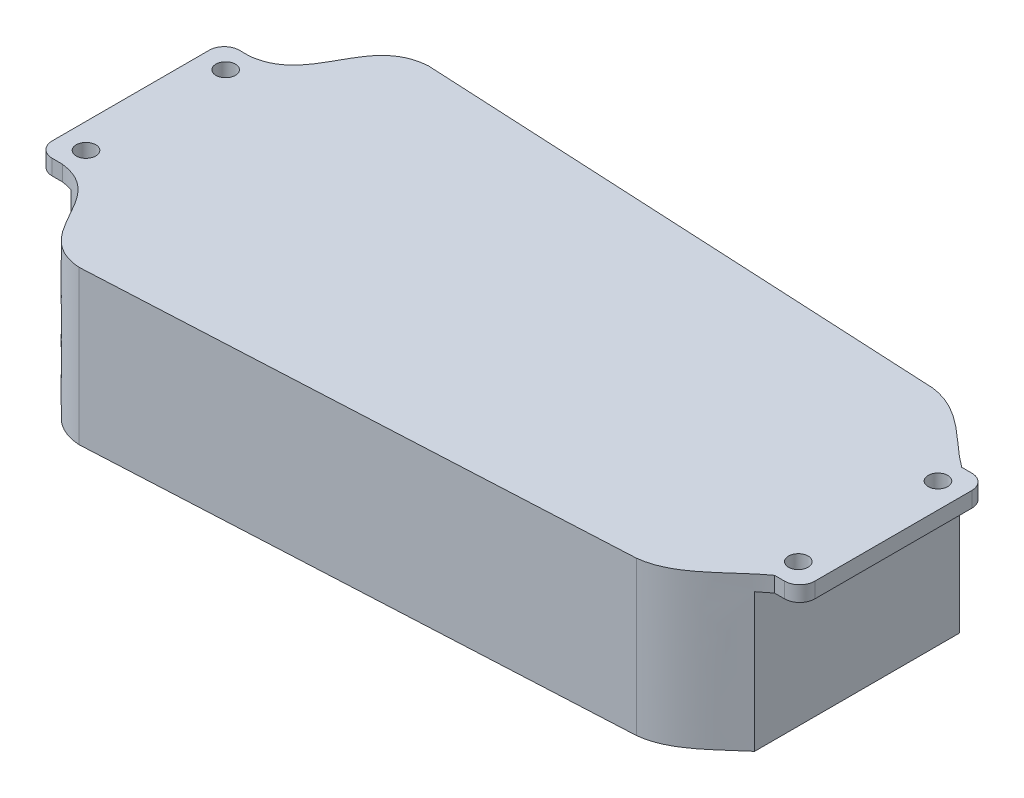
SolidWorks part; units mm, degrees
ref_plane "Front Plane" through (0, 0, 0) normal (0, 0, 1) x (1, 0, 0)
ref_plane "Top Plane" through (0, 0, 0) normal (0, 1, 0) x (1, 0, 0)
ref_plane "Right Plane" through (0, 0, 0) normal (1, 0, 0) x (0, 0, -1)
sketch "Sketch1" plane through (0, 0, 0) normal (0, 1, 0) x (1, 0, 0)
  line L0 (-77.2974, -66.9431) -> (112.638, -57.3431)
  line L2 (-121.2974, 23.6569) -> (-121.2974, -32.5431)
  line L4 (151.7026, 23.6569) -> (151.7026, -32.5431)
  line L5 (-115.7974, -37.9431) -> (-115.8974, -37.9431)
  line L6 (-115.7974, -37.9431) -> (-112.2974, -37.9431)
  line L7 (-77.2974, 58.0569) -> (112.638, 48.4569)
  line L8 (146.2026, -37.9431) -> (142.7026, -37.9431)
  line L9 (-115.7974, 29.0569) -> (-112.2974, 29.0569)
  line L10 (-115.7974, 29.0569) -> (-115.8974, 29.0569)
  line L11 (146.2026, 29.0569) -> (142.7026, 29.0569)
  line L12 (146.2026, 29.0569) -> (146.3026, 29.0569)
  line L13 (146.2026, -37.9431) -> (146.3026, -37.9431)
  circle A0 centre (-112.2974, 20.5569) radius 3.5
  circle A1 centre (-112.2974, -29.4431) radius 3.5
  circle A2 centre (142.7026, -29.4431) radius 3.5
  circle A3 centre (142.7026, 20.5569) radius 3.5
  arc A4 (-115.8974, -37.9431) -> (-121.2974, -32.5431) centre (-115.8974, -32.5431) cw
  arc A5 (-115.8974, 29.0569) -> (-121.2974, 23.6569) centre (-115.8974, 23.6569) ccw
  arc A6 (146.3026, -37.9431) -> (151.7026, -32.5431) centre (146.3026, -32.5431) ccw
  arc A7 (146.3026, 29.0569) -> (151.7026, 23.6569) centre (146.3026, 23.6569) cw
  spline S0 degree 3 poles (-77.2974, 58.0569) (-97.4783, 56.5585) (-92.6699, 31.2994) (-112.2974, 29.0569) knots 0 0 0 0 1 1 1 1
  spline S1 degree 3 poles (-77.2974, -66.9431) (-97.4783, -65.4448) (-92.6699, -40.1856) (-112.2974, -37.9431) knots 0 0 0 0 1 1 1 1
  spline S2 degree 3 poles (112.638, 48.4569) (125.0826, 47.1415) (133.2878, 35.7758) (142.7026, 29.0569) knots 0 0 0 0 1 1 1 1
  spline S3 degree 3 poles (112.638, -57.3431) (125.0826, -56.0277) (133.2878, -44.662) (142.7026, -37.9431) knots 0 0 0 0 1 1 1 1
  point P8 (-121.2974, -4.4431)
  point P25 (-114.0474, 29.0569)
  dimension "D6" = 7
  dimension "D7" = 7
  dimension "D2" = 5.4
  dimension "D3" = 50
  dimension "D4" = 25
  dimension "D5" = 39.0646
  dimension "D12" = 8.5
extrude "Boss-Extrude2" add sketch "Sketch1" against normal blind 55
sketch "Sketch7" plane through (-121.2974, 0, 0) normal (-1, 0, 0) x (0, 0, 1)
  line L0 (-23.6569, 0) -> (32.5431, 0) construction
  line L1 (-30.1667, -5.5) -> (38.8329, -5.5)
  line L2 (-30.1667, -5.5) -> (-30.1667, -55.9156)
  line L3 (-30.1667, -55.9156) -> (38.8329, -55.9156)
  line L4 (38.8329, -5.5) -> (38.8329, -55.9156)
  dimension "D1" = 68.9997
  dimension "D2" = 5.5
extrude "Cut-Extrude5" cut sketch "Sketch7" against normal blind 13
sketch "Sketch19" plane through (151.7026, 0, 0) normal (1, 0, 0) x (0, 0, -1)
  line L0 (-32.5431, 0) -> (23.6569, 0) construction
  line L1 (-42.5272, -5.5) -> (32.3322, -5.5)
  line L2 (-42.5272, -5.5) -> (-42.5272, -66.2251)
  line L3 (-42.5272, -66.2251) -> (32.3322, -66.2251)
  line L4 (32.3322, -5.5) -> (32.3322, -66.2251)
  dimension "D1" = 5.5
extrude "Cut-Extrude7" cut sketch "Sketch19" against normal blind 13
